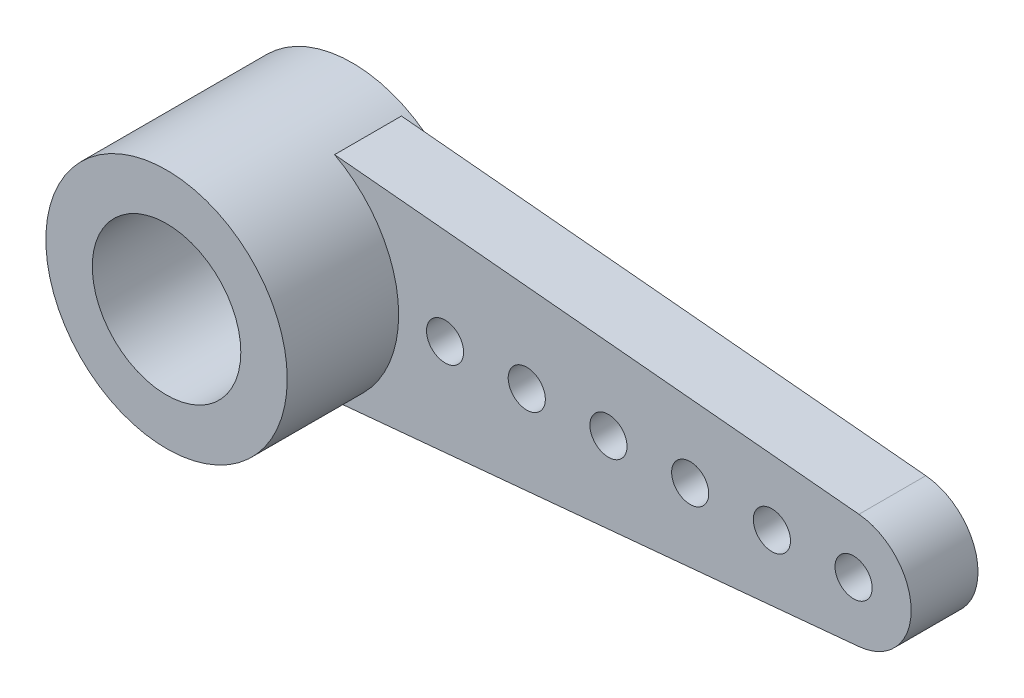
SolidWorks part; units mm, degrees
ref_plane "Ön Düzlem" through (0, 0, 0) normal (0, 0, 1) x (1, 0, 0)
ref_plane "Üst Düzlem" through (0, 0, 0) normal (0, 1, 0) x (1, 0, 0)
ref_plane "Sağ Düzlem" through (0, 0, 0) normal (1, 0, 0) x (0, 0, -1)
sketch "Sketch1" plane through (0, 0, 0) normal (0, 0, 1) x (1, 0, 0)
  line L0 (1.5252, 2.8699) -> (15.645, 1.5432)
  line L1 (0, 0) -> (0, 4.8627) construction
  line L2 (0, 0) -> (0, -5.6571) construction
  line L4 (1.5252, -2.8699) -> (15.645, -1.5432)
  arc A1 (15.645, -1.5432) -> (15.645, 1.5432) centre (15.5, 0) ccw
  arc A5 (1.5252, 2.8699) -> (1.5252, -2.8699) centre (0, 0) ccw
  dimension "D2" = 3.1
  dimension "D3" = 3.25
  dimension "D1" = 15.5
extrude "Boss-Extrude1" add sketch "Sketch1" along normal blind 1.8 contours A5 L4 A1 L0
sketch "Sketch2" plane through (0, 0, 0) normal (0, 0, 1) x (1, 0, 0)
  circle A0 centre (0, 0) radius 3.25
  circle A1 centre (0, 0) radius 2.5
extrude "Boss-Extrude3" add sketch "Sketch2" against normal blind 0.2 contours A1 | A0
sketch "Sketch5" plane through (0, 0, 1.8) normal (0, 0, 1) x (1, 0, 0)
  circle A0 centre (0, 0) radius 3.25
  circle A1 centre (0, 0) radius 2
extrude "Boss-Extrude4" add sketch "Sketch5" along normal blind 3
sketch "Sketch6" plane through (0, 0, 0) normal (0, 0, 1) x (1, 0, 0)
  circle A0 centre (0, 0) radius 1.5
extrude "Cut-Extrude1" cut sketch "Sketch6" along normal up to next
sketch "Sketch8" plane through (0, 0, 0) normal (0, 0, 1) x (1, 0, 0)
  circle A0 centre (15.5, 0) radius 0.5
  circle A1 centre (13.3, 0) radius 0.5
  circle A2 centre (11.1, 0) radius 0.5
  circle A3 centre (8.9, 0) radius 0.5
  circle A4 centre (6.7, 0) radius 0.5
  circle A5 centre (4.5, 0) radius 0.5
  dimension "D3" = 6
extrude "Cut-Extrude2" cut sketch "Sketch8" along normal up to next
